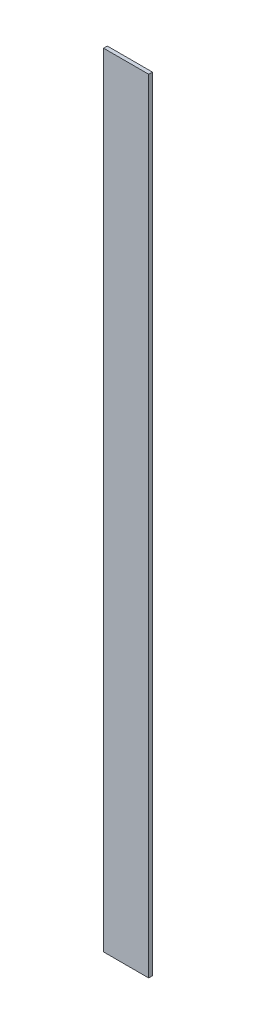
SolidWorks part; units mm, degrees
ref_plane "Front Plane" through (0, 0, 0) normal (0, 0, 1) x (1, 0, 0)
ref_plane "Top Plane" through (0, 0, 0) normal (0, 1, 0) x (1, 0, 0)
ref_plane "Right Plane" through (0, 0, 0) normal (1, 0, 0) x (0, 0, -1)
sketch "Sketch2" plane through (0, 0, 0) normal (0, 1, 0) x (1, 0, 0)
  line L1 (0, 0) -> (38.1, 0)
  line L2 (0, 0) -> (0, 3.175)
  line L3 (0, 3.175) -> (38.1, 3.175)
  line L4 (38.1, 0) -> (38.1, 3.175)
  dimension "D1" = 38.1
  dimension "D2" = 3.175
extrude "Boss-Extrude1" add sketch "Sketch2" along normal blind 660.4
